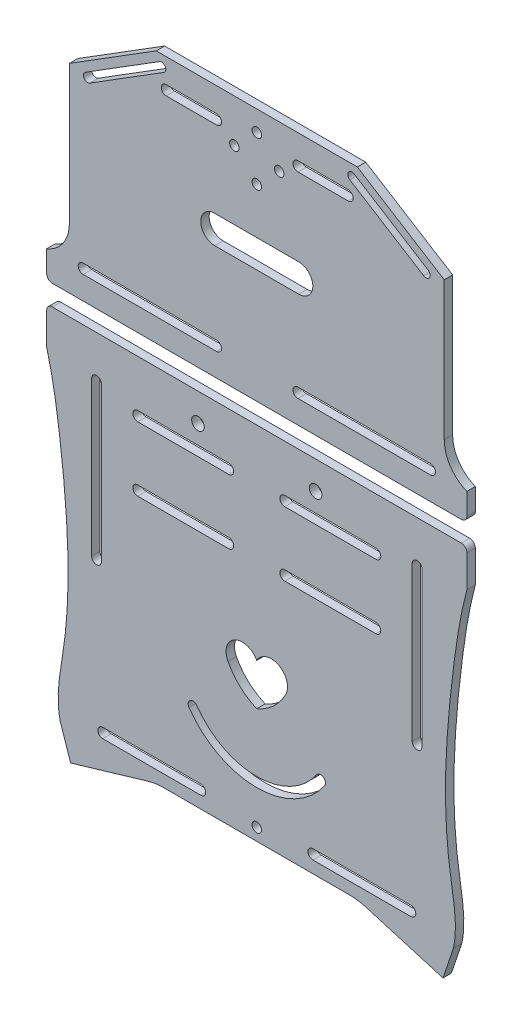
SolidWorks part; units mm, degrees
ref_plane "前视基准面" through (0, 0, 0) normal (0, 0, 1) x (1, 0, 0)
ref_plane "上视基准面" through (0, 0, 0) normal (0, 1, 0) x (1, 0, 0)
ref_plane "右视基准面" through (0, 0, 0) normal (1, 0, 0) x (0, 0, -1)
sketch "草图1" plane through (0, 0, 0) normal (0, 0, 1) x (1, 0, 0)
  line L0 (0, 148.5) -> (0, -94.9538) construction
  line L1 (105, -148.5) -> (-105, -148.5) construction
  line L2 (105, -148.5) -> (105, 148.5) construction
  line L3 (105, 148.5) -> (-105, 148.5) construction
  line L4 (-105, -148.5) -> (-105, 148.5) construction
  line L5 (105, -148.5) -> (-105, 148.5) construction
  line L6 (105, 148.5) -> (-105, -148.5) construction
  line L7 (35.8892, 121.6645) -> (-35.8892, 121.6645)
  line L8 (-35.8892, 121.6645) -> (-66.9017, 102.292)
  line L9 (-75, 40.9339) -> (-75, 31.2613)
  line L10 (-66.9017, 102.292) -> (-66.9017, 52.8701)
  line L11 (75, 40.9339) -> (75, 31.2613)
  line L12 (66.9017, 102.292) -> (66.9017, 52.8701)
  line L13 (35.8892, 121.6645) -> (66.9017, 102.292)
  line L14 (-75, 31.2613) -> (75, 31.2613)
  line L15 (-60, -148.5) -> (-60, -91.8129)
  line L16 (-75, 23.94) -> (75, 23.94)
  line L17 (-75, 23.94) -> (-75, 10.5626)
  line L18 (-38.8455, -105.5906) -> (-66.4608, -113.7617)
  line L19 (-66.4608, -113.7617) -> (-70.1743, -102.7328)
  line L20 (75, 23.94) -> (75, 10.5626)
  line L21 (66.4608, -113.7617) -> (70.1743, -102.7328)
  line L22 (38.8455, -105.5906) -> (66.4608, -113.7617)
  line L23 (-105, 93.0519) -> (105, 93.0519)
  line L24 (-105, 63.0519) -> (105, 63.0519)
  line L25 (-105, -90.0629) -> (-70.5337, -90.0629)
  line L26 (-105, -60.0629) -> (-67.4027, -60.0629)
  line L27 (60, -148.5) -> (60, 148.5)
  line L28 (-60, -58.3129) -> (-45, -58.3129)
  line L29 (-60, -61.8129) -> (-45, -61.8129)
  line L30 (-36, -58.3129) -> (-21, -58.3129)
  line L31 (-36, -61.8129) -> (-21, -61.8129)
  line L32 (-60, -88.3129) -> (-45, -88.3129)
  line L33 (-60, -91.8129) -> (-45, -91.8129)
  line L34 (-36, -88.3129) -> (-21, -88.3129)
  line L35 (-36, -91.8129) -> (-21, -91.8129)
  line L36 (-60, -58.3129) -> (-60, 148.5)
  line L37 (-19.25, -90.0629) -> (105, -90.0629)
  line L38 (-19.25, -60.0629) -> (19.25, -60.0629)
  line L39 (-60, -88.3129) -> (-60, -61.8129)
  line L40 (21, -58.3129) -> (36, -58.3129)
  line L41 (45, -58.3129) -> (60, -58.3129)
  line L42 (60, -61.8129) -> (45, -61.8129)
  line L43 (36, -61.8129) -> (21, -61.8129)
  line L44 (21, -88.3129) -> (36, -88.3129)
  line L45 (21, -91.8129) -> (36, -91.8129)
  line L46 (45, -88.3129) -> (60, -88.3129)
  line L47 (45, -91.8129) -> (60, -91.8129)
  line L48 (37.75, -60.0629) -> (43.25, -60.0629)
  line L49 (58.25, -60.0629) -> (105, -60.0629)
  line L50 (-60, 94.8019) -> (-45, 94.8019)
  line L51 (-36, 94.8019) -> (-21, 94.8019)
  line L52 (-60, 91.3019) -> (-45, 91.3019)
  line L53 (-36, 91.3019) -> (-21, 91.3019)
  line L54 (-60, 64.8019) -> (-45, 64.8019)
  line L55 (-60, 61.3019) -> (-45, 61.3019)
  line L56 (-36, 64.8019) -> (-21, 64.8019)
  line L57 (-36, 61.3019) -> (-21, 61.3019)
  line L58 (21, 94.8019) -> (36, 94.8019)
  line L59 (21, 91.3019) -> (36, 91.3019)
  line L60 (45, 94.8019) -> (60, 94.8019)
  line L61 (45, 91.3019) -> (60, 91.3019)
  line L62 (21, 61.3019) -> (36, 61.3019)
  line L63 (21, 64.8019) -> (36, 64.8019)
  line L64 (45, 61.3019) -> (60, 61.3019)
  line L65 (45, 64.8019) -> (60, 64.8019)
  line L66 (-33.1709, -104.7687) -> (33.1709, -104.7687)
  line L67 (0, -104.7687) -> (0, -148.5) construction
  arc A0 (-75, 40.9339) -> (-66.9017, 52.8701) centre (-79.7474, 52.8701) ccw
  arc A1 (75, 40.9339) -> (66.9017, 52.8701) centre (79.7474, 52.8701) cw
  arc A3 (-60, -88.3129) -> (-60, -91.8129) centre (-60, -90.0629) ccw
  arc A4 (-60, -58.3129) -> (-60, -61.8129) centre (-60, -60.0629) ccw
  circle A5 centre (-60, 63.0519) radius 1.75
  circle A6 centre (-60, 93.0519) radius 1.75
  circle A7 centre (60, 93.0519) radius 1.75
  circle A8 centre (60, 63.0519) radius 1.75
  arc A9 (60, -91.8129) -> (60, -88.3129) centre (60, -90.0629) ccw
  arc A10 (60, -61.8129) -> (60, -58.3129) centre (60, -60.0629) ccw
  arc A11 (-36, -58.3129) -> (-36, -61.8129) centre (-36, -60.0629) ccw
  arc A12 (-36, -88.3129) -> (-36, -91.8129) centre (-36, -90.0629) ccw
  arc A13 (36, -61.8129) -> (36, -58.3129) centre (36, -60.0629) ccw
  arc A14 (36, -91.8129) -> (36, -88.3129) centre (36, -90.0629) ccw
  arc A15 (-45, -61.8129) -> (-45, -58.3129) centre (-45, -60.0629) ccw
  arc A16 (-21, -61.8129) -> (-21, -58.3129) centre (-21, -60.0629) ccw
  arc A17 (-45, -91.8129) -> (-45, -88.3129) centre (-45, -90.0629) ccw
  arc A18 (-21, -91.8129) -> (-21, -88.3129) centre (-21, -90.0629) ccw
  arc A19 (45, -58.3129) -> (45, -61.8129) centre (45, -60.0629) ccw
  arc A20 (21, -58.3129) -> (21, -61.8129) centre (21, -60.0629) ccw
  arc A21 (21, -88.3129) -> (21, -91.8129) centre (21, -90.0629) ccw
  arc A22 (45, -88.3129) -> (45, -91.8129) centre (45, -90.0629) ccw
  circle A23 centre (-36, 93.0519) radius 1.75
  circle A24 centre (-36, 63.0519) radius 1.75
  circle A25 centre (36, 93.0519) radius 1.75
  circle A26 centre (36, 63.0519) radius 1.75
  circle A27 centre (-45, 93.0519) radius 1.75
  circle A28 centre (-21, 93.0519) radius 1.75
  circle A29 centre (-45, 63.0519) radius 1.75
  circle A30 centre (-21, 63.0519) radius 1.75
  circle A31 centre (21, 93.0519) radius 1.75
  circle A32 centre (21, 63.0519) radius 1.75
  circle A33 centre (45, 93.0519) radius 1.75
  circle A34 centre (45, 63.0519) radius 1.75
  arc A35 (33.1709, -104.7687) -> (38.8455, -105.5906) centre (33.1709, -124.7687) cw
  arc A36 (-33.1709, -104.7687) -> (-38.8455, -105.5906) centre (-33.1709, -124.7687) ccw
  spline S0 degree 3 poles (-75, 10.5626) (-72.6959, 1.9073) (-70.3396, -13.3728) (-67.1028, -43.6255) (-66.7657, -72.9327) (-71.8903, -95.1489) (-70.1743, -102.7328) knots 0 0 0 0 0.235247 0.406294 0.801186 1 1 1 1
  spline S1 degree 3 poles (75, 10.5626) (72.6959, 1.9073) (70.3396, -13.3728) (67.1028, -43.6255) (66.7657, -72.9327) (71.8903, -95.1489) (70.1743, -102.7328) knots 0 0 0 0 0.235247 0.406294 0.801186 1 1 1 1
  point P0 (0, 0)
  point P27 (0, 121.6645)
  point P42 (0, -94.0966)
  dimension "D1" = 60
  dimension "D4" = 20
  dimension "D5" = 24
  dimension "D7" = 24
  dimension "D9" = 15
  dimension "D10" = 15
  dimension "D13" = 24
  dimension "D17" = 15
  dimension "D2" = 30
  dimension "D3" = 30
  dimension "D6" = 24
  dimension "D8" = 24
  dimension "D11" = 15
  dimension "D12" = 15
  dimension "D14" = 24
  dimension "D15" = 24
  dimension "D16" = 24
  dimension "D18" = 15
  dimension "D19" = 15
  dimension "D20" = 15
  dimension "D21" = 15
  dimension "D22" = 15
  dimension "D23" = 15
  dimension "D24" = 15
  dimension "D25" = 15
  dimension "D26" = 15
  dimension "D27" = 15
  dimension "D28" = 15
  dimension "D29" = 3.5
  dimension "D30" = 3.5
  dimension "D31" = 3.5
extrude "凸台-拉伸1" add sketch "草图1" along normal blind 3
sketch "草图7" plane through (0, 0, 0) normal (0, 0, -1) x (-1, 0, 0)
  line L0 (0, 121.6645) -> (0, -104.7687) construction
  line L1 (-35.8892, 121.6645) -> (35.8892, 121.6645) construction
  line L2 (33.1709, -104.7687) -> (-33.1709, -104.7687) construction
  line L3 (0, 41.2613) -> (-21, 41.2613) construction
  line L4 (0, 41.2613) -> (21, 41.2613) construction
  line L5 (0, 13.94) -> (-21, 13.94) construction
  line L6 (0, 13.94) -> (21, 13.94) construction
  line L7 (75, 23.94) -> (-75, 23.94) construction
  line L8 (75, 31.2613) -> (-75, 31.2613) construction
  circle A0 centre (-21, 41.2613) radius 1.75
  circle A1 centre (21, 41.2613) radius 1.75
  circle A2 centre (-21, 13.94) radius 2.25
  circle A3 centre (21, 13.94) radius 2.25
  dimension "D1" = 10
  dimension "D2" = 10
extrude "切除-拉伸2" cut sketch "草图7" against normal through all
sketch "草图9" plane through (0, 0, 3) normal (0, 0, 1) x (1, 0, 0)
  line L0 (-70.7828, -98.747) -> (70.7828, -98.747) construction
  line L1 (0, -98.747) -> (0, -104.7687) construction
  line L2 (55, -100.497) -> (20, -100.497)
  line L3 (-55, -96.997) -> (-20, -96.997)
  line L4 (-55, -100.497) -> (-20, -100.497)
  line L5 (-33.1709, -104.7687) -> (33.1709, -104.7687) construction
  line L6 (55, -96.997) -> (20, -96.997)
  arc A0 (-55, -96.997) -> (-55, -100.497) centre (-55, -98.747) ccw
  arc A1 (-20, -100.497) -> (-20, -96.997) centre (-20, -98.747) ccw
  arc A2 (20, -100.497) -> (20, -96.997) centre (20, -98.747) cw
  arc A3 (55, -96.997) -> (55, -100.497) centre (55, -98.747) cw
  spline S0 degree 3 poles (-75, 10.5626) (-72.6959, 1.9073) (-70.3396, -13.3728) (-67.1028, -43.6255) (-66.7657, -72.9327) (-71.8903, -95.1489) (-70.1743, -102.7328) knots 0 0 0 0 0.235247 0.406294 0.801186 1 1 1 1 construction
  spline S1 degree 3 poles (75, 10.5626) (72.6959, 1.9073) (70.3396, -13.3728) (67.1028, -43.6255) (66.7657, -72.9327) (71.8903, -95.1489) (70.1743, -102.7328) knots 0 0 0 0 0.235247 0.406294 0.801186 1 1 1 1 construction
  dimension "D1" = 35
  dimension "D2" = 20
extrude "切除-拉伸4" cut sketch "草图9" against normal blind 3
sketch "草图10" plane through (0, 0, 3) normal (0, 0, 1) x (1, 0, 0)
  line L0 (-21, -60.0629) -> (-21, -90.0629) construction
  line L1 (21, -60.0629) -> (21, -90.0629) construction
  line L2 (-21, -75.0629) -> (-17.5, -75.0629) construction
  line L4 (12.5, -80.0629) -> (-12.5, -80.0629)
  line L6 (12.5, -70.0629) -> (-12.5, -70.0629)
  line L11 (17.5, -75.0629) -> (21, -75.0629) construction
  arc A0 (-12.5, -70.0629) -> (-12.5, -80.0629) centre (-12.5, -75.0629) ccw
  arc A1 (12.5, -80.0629) -> (12.5, -70.0629) centre (12.5, -75.0629) ccw
  point P11 (0, -75.0629)
extrude "切除-拉伸5" cut sketch "草图10" against normal blind 3
sketch "草图11" plane through (0, 0, 3) normal (0, 0, 1) x (1, 0, 0)
  line L0 (-21, 93.0519) -> (-21, 63.0519) construction
  line L1 (21, 93.0519) -> (21, 63.0519) construction
  line L2 (-21, 78.0519) -> (-20, 78.0519) construction
  line L4 (15, 73.0519) -> (-15, 73.0519)
  line L6 (15, 83.0519) -> (-15, 83.0519)
  line L10 (20, 78.0519) -> (21, 78.0519) construction
  arc A0 (-15, 83.0519) -> (-15, 73.0519) centre (-15, 78.0519) ccw
  arc A1 (15, 73.0519) -> (15, 83.0519) centre (15, 78.0519) ccw
  point P10 (0, 78.0519)
  dimension "D1" = 30
extrude "切除-拉伸8" cut sketch "草图11" against normal blind 3
sketch "草图12" plane through (0, 0, 3) normal (0, 0, 1) x (1, 0, 0)
  line L0 (0, 121.6645) -> (0, 83.0519) construction
  line L1 (35.8892, 121.6645) -> (-35.8892, 121.6645) construction
  line L2 (15, 83.0519) -> (-15, 83.0519) construction
  circle A0 centre (0, 106.3718) radius 11 construction
  circle A1 centre (0, 106.3718) radius 8 construction
  circle A2 centre (0, 114.3718) radius 1.7
  circle A3 centre (0, 98.3718) radius 1.7
  circle A4 centre (8, 106.3718) radius 1.7
  circle A5 centre (-8, 106.3718) radius 1.7
extrude "切除-拉伸9" cut sketch "草图12" against normal blind 3
sketch "草图13" plane through (0, 0, 3) normal (0, 0, 1) x (1, 0, 0)
  line L0 (0, -104.7687) -> (0, -80.0629) construction
  line L1 (-33.1709, -104.7687) -> (33.1709, -104.7687) construction
  line L2 (-12.5, -80.0629) -> (12.5, -80.0629) construction
  circle A0 centre (0, -92.4158) radius 8 construction
  circle A1 centre (0, -84.4158) radius 1.7
  circle A2 centre (8, -92.4158) radius 1.7
  circle A3 centre (0, -100.4158) radius 1.7
  circle A4 centre (-8, -92.4158) radius 1.7
extrude "切除-拉伸11" cut sketch "草图13" against normal blind 3
sketch "草图14" plane through (0, 0, 3) normal (0, 0, 1) x (1, 0, 0)
  line L0 (0, 23.94) -> (0, -104.7687) construction
  line L1 (-55.4755, 8.9197) -> (-55.4755, -46.0803)
  line L2 (-58.9755, 8.9197) -> (-58.9755, -46.0803)
  line L3 (-75, 23.94) -> (75, 23.94) construction
  line L4 (-33.1709, -104.7687) -> (33.1709, -104.7687) construction
  line L5 (58.9755, 8.9197) -> (58.9755, -46.0803)
  line L6 (55.4755, 8.9197) -> (55.4755, -46.0803)
  arc A0 (-55.4755, 8.9197) -> (-58.9755, 8.9197) centre (-57.2255, 8.9197) ccw
  arc A1 (-58.9755, -46.0803) -> (-55.4755, -46.0803) centre (-57.2255, -46.0803) ccw
  arc A2 (58.9755, -46.0803) -> (55.4755, -46.0803) centre (57.2255, -46.0803) cw
  arc A3 (55.4755, 8.9197) -> (58.9755, 8.9197) centre (57.2255, 8.9197) cw
extrude "切除-拉伸12" cut sketch "草图14" against normal through all
fillet "圆角1" radius 2 2 edges at (75, 31.2613, 1.5) (-75, 31.2613, 1.5)
fillet "圆角2" radius 2 2 edges at (-75, 23.94, 1.5) (75, 23.94, 1.5)
sketch "草图15" plane through (0, 0, 0) normal (0, 0, -1) x (-1, 0, 0)
  line L0 (0, 121.6645) -> (0, 31.2613) construction
  line L1 (-35.8892, 121.6645) -> (35.8892, 121.6645) construction
  line L2 (73, 31.2613) -> (-73, 31.2613) construction
  line L3 (-27.5188, 121.6645) -> (-63.6963, 99.0657) construction
  line L4 (-35.8892, 121.6645) -> (-66.9017, 102.292) construction
  line L5 (-61.1842, 102.4035) -> (-34.7748, 118.9006)
  line L6 (-59.5948, 99.8591) -> (-33.1854, 116.3562)
  line L7 (27.5188, 121.6645) -> (63.6963, 99.0657) construction
  line L8 (59.5948, 99.8591) -> (33.1854, 116.3562)
  line L9 (61.1842, 102.4035) -> (34.7748, 118.9006)
  arc A0 (-61.1842, 102.4035) -> (-59.5948, 99.8591) centre (-60.3895, 101.1313) ccw
  arc A1 (-33.1854, 116.3562) -> (-34.7748, 118.9006) centre (-33.9801, 117.6284) ccw
  arc A2 (33.1854, 116.3562) -> (34.7748, 118.9006) centre (33.9801, 117.6284) cw
  arc A3 (61.1842, 102.4035) -> (59.5948, 99.8591) centre (60.3895, 101.1313) cw
extrude "切除-拉伸13" cut sketch "草图15" against normal through all
sketch "草图16" plane through (0, 0, 0) normal (0, 0, -1) x (-1, 0, 0)
  line L0 (0, 121.6645) -> (0, 31.2613) construction
  line L1 (-35.8892, 121.6645) -> (35.8892, 121.6645) construction
  line L2 (73, 31.2613) -> (-73, 31.2613) construction
  line L3 (-21, 41.2613) -> (-66.71, 41.2613) construction
  line L4 (-62, 43.0113) -> (-32, 43.0113)
  line L5 (-62, 39.5113) -> (-32, 39.5113)
  line L6 (21, 41.2613) -> (66.71, 41.2613) construction
  line L7 (62, 39.5113) -> (32, 39.5113)
  line L8 (62, 43.0113) -> (32, 43.0113)
  line L9 (-75, 40.9339) -> (-75, 33.2613) construction
  arc A0 (-62, 43.0113) -> (-62, 39.5113) centre (-62, 41.2613) ccw
  arc A1 (-32, 39.5113) -> (-32, 43.0113) centre (-32, 41.2613) ccw
  arc A2 (32, 39.5113) -> (32, 43.0113) centre (32, 41.2613) cw
  arc A3 (62, 43.0113) -> (62, 39.5113) centre (62, 41.2613) cw
  dimension "D2" = 13
sketch "草图17" plane through (0, 0, 0) normal (0, 0, -1) x (-1, 0, 0)
  text T0 "Y" font "黑体" height in points 72
extrude "切除-拉伸15" cut sketch "草图17" against normal through all
sketch "草图18" plane through (0, 0, 0) normal (0, 0, -1) x (-1, 0, 0)
  text T0 "H" font "黑体" height in points 72
extrude "切除-拉伸16" cut sketch "草图18" against normal through all
sketch "草图20" plane through (0, 0, 0) normal (0, 0, -1) x (-1, 0, 0)
  line L0 (-66.9017, 102.292) -> (-66.9017, 52.8701) construction
  line L1 (-66.9017, 95.8596) -> (66.9017, 95.8596)
  line L2 (-66.9017, 95.8596) -> (-66.9017, 52.8701)
  line L3 (-66.9017, 52.8701) -> (66.9017, 52.8701)
  line L4 (66.9017, 95.8596) -> (66.9017, 52.8701)
extrude "凸台-拉伸2" add sketch "草图20" against normal blind 3
sketch "草图21" plane through (0, 0, 0) normal (0, 0, -1) x (-1, 0, 0)
  line L1 (-64.7663, -56.4228) -> (64.4409, -56.4228)
  line L2 (-64.7663, -56.4228) -> (-64.7663, -95.2117)
  line L3 (-64.7663, -95.2117) -> (64.4409, -95.2117)
  line L4 (64.4409, -56.4228) -> (64.4409, -95.2117)
extrude "凸台-拉伸3" add sketch "草图21" against normal blind 3
sketch "草图22" plane through (0, 0, 0) normal (0, 0, -1) x (-1, 0, 0)
  line L1 (-46.7188, -3.1128) -> (-25.8503, -3.1128)
  line L2 (-46.7188, -3.1128) -> (-46.7188, -34.3233)
  line L3 (-46.7188, -34.3233) -> (-25.8503, -34.3233)
  line L4 (-25.8503, -3.1128) -> (-25.8503, -34.3233)
  line L5 (28.8143, -3.1128) -> (49.8675, -3.1128)
  line L6 (28.8143, -3.1128) -> (28.8143, -33.2152)
  line L7 (28.8143, -33.2152) -> (49.8675, -33.2152)
  line L8 (49.8675, -3.1128) -> (49.8675, -33.2152)
extrude "凸台-拉伸4" add sketch "草图22" against normal blind 3
sketch "草图24" plane through (0, 0, 0) normal (0, 0, -1) x (-1, 0, 0)
  line L1 (-64.9961, 44.3276) -> (-28.6954, 44.3276)
  line L2 (-64.9961, 44.3276) -> (-64.9961, 38.3743)
  line L3 (-64.9961, 38.3743) -> (-28.6954, 38.3743)
  line L4 (-28.6954, 44.3276) -> (-28.6954, 38.3743)
  line L5 (29.2405, 44.3276) -> (65.8315, 44.3276)
  line L6 (29.2405, 44.3276) -> (29.2405, 38.3743)
  line L7 (29.2405, 38.3743) -> (65.8315, 38.3743)
  line L8 (65.8315, 44.3276) -> (65.8315, 38.3743)
extrude "凸台-拉伸5" add sketch "草图24" against normal blind 3
sketch "草图25" plane through (0, 0, 0) normal (0, 0, -1) x (-1, 0, 0)
  line L0 (-32.6582, 113.0113) -> (-14.6582, 113.0113)
  line L1 (-32.6582, 109.5113) -> (-14.6582, 109.5113)
  line L2 (-21, 41.2613) -> (21, 41.2613)
  line L3 (-0.3165, 111.2613) -> (0, 41.2613) construction
  line L4 (14.3418, 113.0113) -> (32.3418, 113.0113)
  line L5 (32.3418, 41.2613) -> (-32.6582, 41.2613)
  line L6 (32.3418, 41.2613) -> (32.3418, 111.2613)
  line L8 (-32.6582, 41.2613) -> (-32.6582, 111.2613)
  line L9 (32.3418, 41.2613) -> (-32.6582, 111.2613) construction
  line L10 (30.7168, 109.5113) -> (-32.6582, 41.2613) construction
  line L11 (14.3418, 109.5113) -> (32.3418, 109.5113)
  line L12 (32.3418, 76.2613) -> (-32.6582, 76.2613) construction
  line L13 (12.5918, 111.2613) -> (-12.9082, 111.2613)
  line L14 (12.5918, 41.2613) -> (-12.9082, 41.2613)
  line L15 (14.3418, 43.0113) -> (32.3418, 43.0113)
  line L16 (14.3418, 39.5113) -> (32.3418, 39.5113)
  line L17 (-32.6582, 43.0113) -> (-14.6582, 43.0113)
  line L18 (-32.6582, 39.5113) -> (-14.6582, 39.5113)
  circle A0 centre (-32.6582, 111.2613) radius 1.75
  arc A1 (32.3418, 109.5113) -> (32.3418, 113.0113) centre (32.3418, 111.2613) ccw
  arc A2 (-14.6582, 109.5113) -> (-14.6582, 113.0113) centre (-14.6582, 111.2613) ccw
  arc A3 (14.3418, 113.0113) -> (14.3418, 109.5113) centre (14.3418, 111.2613) ccw
  arc A4 (14.3418, 39.5113) -> (14.3418, 43.0113) centre (14.3418, 41.2613) cw
  arc A5 (-14.6582, 43.0113) -> (-14.6582, 39.5113) centre (-14.6582, 41.2613) cw
  arc A6 (32.3418, 43.0113) -> (32.3418, 39.5113) centre (32.3418, 41.2613) cw
  circle A7 centre (-32.6582, 41.2613) radius 1.75
  point P9 (-0.1582, 76.2613)
  dimension "D1" = 18
  dimension "D2" = 18
extrude "切除-拉伸17" cut sketch "草图25" against normal through all
extrude "切除-拉伸19" cut sketch "草图16" against normal through all
sketch "草图26" plane through (0, 0, 0) normal (0, 0, -1) x (-1, 0, 0)
  line L0 (0, 121.6645) -> (0, -104.7687) construction
  line L1 (-35.8892, 121.6645) -> (35.8892, 121.6645) construction
  line L2 (33.1709, -104.7687) -> (-33.1709, -104.7687) construction
  line L4 (15, 71.877) -> (-15, 71.877)
  line L6 (15, 81.877) -> (-15, 81.877)
  arc A0 (-15, 81.877) -> (-15, 71.877) centre (-15, 76.877) ccw
  arc A1 (15, 71.877) -> (15, 81.877) centre (15, 76.877) ccw
  point P6 (0, 76.877)
extrude "切除-拉伸20" cut sketch "草图26" against normal through all
sketch "草图27" plane through (0, 0, 0) normal (0, 0, -1) x (-1, 0, 0)
  line L0 (0, 23.94) -> (0, -104.7687) construction
  line L1 (73, 23.94) -> (-73, 23.94) construction
  line L2 (33.1709, -104.7687) -> (-33.1709, -104.7687) construction
  line L3 (-42.5, -15.81) -> (-10, -15.81)
  line L4 (42.5, -17.56) -> (-42.5, -17.56)
  line L5 (42.5, -17.56) -> (42.5, 5.44)
  line L6 (42.5, 5.44) -> (-42.5, 5.44)
  line L7 (-42.5, -17.56) -> (-42.5, 5.44)
  line L8 (42.5, -17.56) -> (-42.5, 5.44) construction
  line L9 (42.5, 5.44) -> (-42.5, -17.56) construction
  line L10 (-42.5, -19.31) -> (-10, -19.31)
  line L11 (-42.5, 7.19) -> (-10, 7.19)
  line L12 (-42.5, 3.69) -> (-10, 3.69)
  line L13 (10, 7.19) -> (42.5, 7.19)
  line L14 (10, 3.69) -> (42.5, 3.69)
  line L15 (10, -15.81) -> (42.5, -15.81)
  line L16 (10, -19.31) -> (42.5, -19.31)
  circle A0 centre (-42.5, 5.44) radius 1.75
  circle A1 centre (-42.5, -17.56) radius 1.75
  circle A2 centre (42.5, 5.44) radius 1.75
  circle A3 centre (42.5, -17.56) radius 1.75
  circle A4 centre (-10, 5.44) radius 1.75
  circle A5 centre (-10, -17.56) radius 1.75
  circle A6 centre (10, -17.56) radius 1.75
  circle A7 centre (10, 5.44) radius 1.75
  point P6 (0, -6.06)
  dimension "D4" = 10
  dimension "D5" = 10
  dimension "D1" = 30
  dimension "D2" = 85
  dimension "D3" = 23
extrude "切除-拉伸21" cut sketch "草图27" against normal through all contours L6 A0 L7 | L7 A0 L6 | A4 L11 A0 L6 | A4 L6 A0 L12 | L6 A4 | L6 A4 | A7 L6 | A7 L6 | L6 A7 L14 A2 | L13 A7 L6 A2 | A2 L6 L5 | L6 A2 L5 | L7 A1 L4 | L4 A1 L7 | A5 L3 A1 L4 | A5 L4 A1 L10 | L4 A5 | L4 A5 | A6 L4 | A6 L4 | L4 A6 L16 A3 | L15 A6 L4 A3 | L4 A3 L5 | L5 A3 L4
sketch "草图28" plane through (0, 0, 0) normal (0, 0, -1) x (-1, 0, 0)
  line L0 (0, 23.94) -> (0, -104.7687) construction
  line L1 (73, 23.94) -> (-73, 23.94) construction
  line L2 (33.1709, -104.7687) -> (-33.1709, -104.7687) construction
  arc A0 (0, -48.8123) -> (-10.2848, -54.2659) centre (-5.1424, -51.5391) ccw
  arc A1 (-10.2848, -54.2659) -> (0, -63.7557) centre (7.9187, -44.8556) ccw
  arc A2 (10.2848, -54.2659) -> (0, -63.7557) centre (-7.9187, -44.8556) cw
  arc A3 (0, -48.8123) -> (10.2848, -54.2659) centre (5.1424, -51.5391) cw
  point P11 (0, -48.8123)
  point P12 (-10.2848, -54.2659)
extrude "切除-拉伸22" cut sketch "草图28" against normal through all
sketch "草图29" plane through (0, 0, 0) normal (0, 0, -1) x (-1, 0, 0)
  line L0 (0, 23.94) -> (0, -104.7687) construction
  line L1 (73, 23.94) -> (-73, 23.94) construction
  line L2 (33.1709, -104.7687) -> (-33.1709, -104.7687) construction
  arc A0 (-21.3687, -73.4908) -> (21.3687, -73.4908) centre (0, -58.7579) ccw
  arc A1 (-24.1996, -75.4426) -> (24.1996, -75.4426) centre (0, -58.7579) ccw
  arc A2 (-21.3687, -73.4908) -> (-24.1996, -75.4426) centre (-22.7842, -74.4667) ccw
  arc A3 (24.1996, -75.4426) -> (21.3687, -73.4908) centre (22.7842, -74.4667) ccw
extrude "切除-拉伸23" cut sketch "草图29" against normal blind 3
